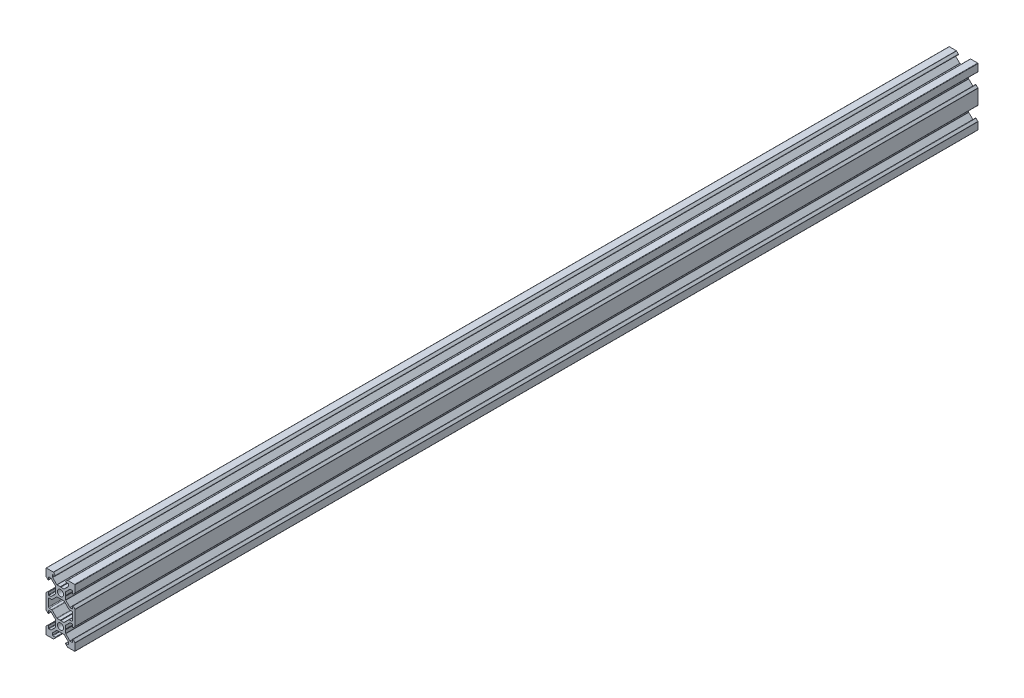
SolidWorks part; units mm, degrees
ref_plane "Front Plane" through (0, 0, 0) normal (0, 0, 1) x (1, 0, 0)
ref_plane "Top Plane" through (0, 0, 0) normal (0, 1, 0) x (1, 0, 0)
ref_plane "Right Plane" through (0, 0, 0) normal (1, 0, 0) x (0, 0, -1)
sketch "Sketch1" plane through (0, 0, 0) normal (0, 0, 1) x (1, 0, 0)
  line L0 (3.5607, 3.5607) -> (10.6317, 10.6317) construction
  line L1 (2.5, -3.5607) -> (-2.5, -3.5607)
  line L2 (3.5607, -2.5) -> (3.5607, 2.5)
  line L3 (2.5, 3.5607) -> (-2.5, 3.5607)
  line L4 (-3.5607, -2.5) -> (-3.5607, 2.5)
  line L5 (3.5607, -3.5607) -> (-3.5607, 3.5607) construction
  line L6 (3.5607, 3.5607) -> (-3.5607, -3.5607) construction
  line L7 (2.5, 3.5607) -> (5.5, 6.5607)
  line L8 (5.5, 6.5607) -> (5.5, 8.2521)
  line L9 (5.5, 8.2521) -> (3.1, 8.2521)
  line L10 (3.1, 8.2521) -> (4.8479, 10)
  line L11 (4.8479, 10) -> (10, 10)
  line L12 (3.5607, 2.5) -> (6.5607, 5.5)
  line L13 (6.5607, 5.5) -> (8.2521, 5.5)
  line L14 (8.2521, 5.5) -> (8.2521, 3.1)
  line L15 (8.2521, 3.1) -> (10, 4.8479)
  line L16 (10, 4.8479) -> (10, 10)
  line L17 (0, -55) -> (0, 55) construction
  line L18 (-3.5607, 3.5607) -> (-10.6317, 10.6317) construction
  line L19 (-10, 4.8479) -> (-10, 10)
  line L20 (-8.2521, 3.1) -> (-10, 4.8479)
  line L21 (-8.2521, 5.5) -> (-8.2521, 3.1)
  line L22 (-6.5607, 5.5) -> (-8.2521, 5.5)
  line L23 (-3.5607, 2.5) -> (-6.5607, 5.5)
  line L24 (-4.8479, 10) -> (-10, 10)
  line L25 (-3.1, 8.2521) -> (-4.8479, 10)
  line L26 (-5.5, 8.2521) -> (-3.1, 8.2521)
  line L27 (-5.5, 6.5607) -> (-5.5, 8.2521)
  line L28 (-2.5, 3.5607) -> (-5.5, 6.5607)
  line L29 (-8.2521, -7) -> (-5.9393, -7)
  line L30 (55, 0) -> (-55, 0) construction
  line L31 (-3.5607, -3.5607) -> (-10.6317, -10.6317) construction
  line L32 (3.5607, -3.5607) -> (10.6317, -10.6317) construction
  line L33 (-2.5, -3.5607) -> (-5.5, -6.5607)
  line L34 (-5.5, -6.5607) -> (-5.9393, -7)
  line L35 (5.5, -6.5607) -> (5.9393, -7)
  line L36 (8.2521, -7) -> (5.9393, -7)
  line L37 (-12.2633, -10) -> (14.5346, -10) construction
  line L38 (-3.5607, -2.5) -> (-6.5607, -5.5)
  line L39 (-6.5607, -5.5) -> (-8.2521, -5.5)
  line L40 (-8.2521, -5.5) -> (-8.2521, -3.1)
  line L41 (-8.2521, -3.1) -> (-10, -4.8479)
  line L42 (-10, -4.8479) -> (-10, -7)
  line L43 (10, -4.8479) -> (10, -7)
  line L44 (8.2521, -3.1) -> (10, -4.8479)
  line L45 (8.2521, -5.5) -> (8.2521, -3.1)
  line L46 (6.5607, -5.5) -> (8.2521, -5.5)
  line L47 (3.5607, -2.5) -> (6.5607, -5.5)
  line L48 (-3.5607, -23.5607) -> (-10.6317, -30.6317) construction
  line L49 (3.5607, -23.5607) -> (-3.5607, -16.4393) construction
  line L50 (3.5607, -16.4393) -> (-3.5607, -23.5607) construction
  line L51 (3.5607, -23.5607) -> (10.6317, -30.6317) construction
  line L52 (2.5, -3.5607) -> (5.5, -6.5607)
  line L53 (2.5, -16.4393) -> (5.5, -13.4393)
  line L54 (3.5607, -17.5) -> (6.5607, -14.5)
  line L55 (6.5607, -14.5) -> (8.2521, -14.5)
  line L56 (8.2521, -14.5) -> (8.2521, -16.9)
  line L57 (8.2521, -16.9) -> (10, -15.1521)
  line L58 (10, -15.1521) -> (10, -13)
  line L59 (-10, -15.1521) -> (-10, -13)
  line L60 (-8.2521, -16.9) -> (-10, -15.1521)
  line L61 (-8.2521, -14.5) -> (-8.2521, -16.9)
  line L62 (-6.5607, -14.5) -> (-8.2521, -14.5)
  line L63 (-3.5607, -17.5) -> (-6.5607, -14.5)
  line L64 (8.2521, -13) -> (5.9393, -13)
  line L65 (5.5, -13.4393) -> (5.9393, -13)
  line L66 (-5.5, -13.4393) -> (-5.9393, -13)
  line L67 (-2.5, -16.4393) -> (-5.5, -13.4393)
  line L68 (-8.2521, -13) -> (-5.9393, -13)
  line L69 (-2.5, -23.5607) -> (-5.5, -26.5607)
  line L70 (-5.5, -26.5607) -> (-5.5, -28.2521)
  line L71 (-5.5, -28.2521) -> (-3.1, -28.2521)
  line L72 (-3.1, -28.2521) -> (-4.8479, -30)
  line L73 (-4.8479, -30) -> (-10, -30)
  line L74 (-3.5607, -22.5) -> (-6.5607, -25.5)
  line L75 (-6.5607, -25.5) -> (-8.2521, -25.5)
  line L76 (-8.2521, -25.5) -> (-8.2521, -23.1)
  line L77 (-8.2521, -23.1) -> (-10, -24.8479)
  line L78 (-10, -24.8479) -> (-10, -30)
  line L79 (10, -24.8479) -> (10, -30)
  line L80 (8.2521, -23.1) -> (10, -24.8479)
  line L81 (8.2521, -25.5) -> (8.2521, -23.1)
  line L82 (6.5607, -25.5) -> (8.2521, -25.5)
  line L83 (3.5607, -22.5) -> (6.5607, -25.5)
  line L84 (4.8479, -30) -> (10, -30)
  line L85 (3.1, -28.2521) -> (4.8479, -30)
  line L86 (5.5, -28.2521) -> (3.1, -28.2521)
  line L87 (5.5, -26.5607) -> (5.5, -28.2521)
  line L88 (2.5, -23.5607) -> (5.5, -26.5607)
  line L89 (-3.5607, -17.5) -> (-3.5607, -22.5)
  line L90 (2.5, -23.5607) -> (-2.5, -23.5607)
  line L91 (3.5607, -17.5) -> (3.5607, -22.5)
  line L92 (2.5, -16.4393) -> (-2.5, -16.4393)
  line L93 (-10, -7) -> (-10, -13)
  line L94 (-8.2521, -13) -> (-8.2521, -7)
  line L95 (8.2521, -13) -> (8.2521, -7)
  line L96 (10, -7) -> (10, -13)
  circle A0 centre (0, 0) radius 2.1
  circle A1 centre (0, -20) radius 2.1
  point P0 (0, 0)
  point P102 (0, -20)
  dimension "D10" = 4.2
  dimension "D11" = 4.2
  dimension "D1" = 1.5
  dimension "D2" = 10
  dimension "D3" = 20
  dimension "D4" = 6.2
  dimension "D5" = 11
  dimension "D6" = 45
  dimension "D7" = 1.5
  dimension "D8" = 10
  dimension "D9" = 5
extrude "Boss-Extrude1" add sketch "Sketch1" along normal blind 622.69
fillet "Fillet1" radius 0.25 64 edges at (5.5, 6.5607, 311.345) (5.5, 8.2521, 311.345) (3.1, 8.2521, 311.345) (4.8479, 10, 311.345) (10, 10, 311.345) (10, 4.8479, 311.345) (8.2521, 3.1, 311.345) (8.2521, 5.5, 311.345) (6.5607, 5.5, 311.345) (3.5607, 2.5, 311.345) (3.5607, -2.5, 311.345) (6.5607, -5.5, 311.345) (8.2521, -5.5, 311.345) (8.2521, -3.1, 311.345) (10, -4.8479, 311.345) (10, -15.1521, 311.345) (8.2521, -16.9, 311.345) (8.2521, -14.5, 311.345) (6.5607, -14.5, 311.345) (3.5607, -17.5, 311.345) (3.5607, -22.5, 311.345) (6.5607, -25.5, 311.345) (8.2521, -25.5, 311.345) (8.2521, -23.1, 311.345) (10, -24.8479, 311.345) (10, -30, 311.345) (4.8479, -30, 311.345) (3.1, -28.2521, 311.345) (5.5, -28.2521, 311.345) (5.5, -26.5607, 311.345) (2.5, -23.5607, 311.345) (-2.5, -23.5607, 311.345) (-5.5, -26.5607, 311.345) (-5.5, -28.2521, 311.345) (-3.1, -28.2521, 311.345) (-4.8479, -30, 311.345) (-10, -30, 311.345) (-10, -24.8479, 311.345) (-8.2521, -23.1, 311.345) (-8.2521, -25.5, 311.345) (-6.5607, -25.5, 311.345) (-3.5607, -22.5, 311.345) (-3.5607, -17.5, 311.345) (-6.5607, -14.5, 311.345) (-8.2521, -14.5, 311.345) (-8.2521, -16.9, 311.345) (-10, -15.1521, 311.345) (-10, -4.8479, 311.345) (-8.2521, -3.1, 311.345) (-8.2521, -5.5, 311.345) (-6.5607, -5.5, 311.345) (-3.5607, -2.5, 311.345) (-3.5607, 2.5, 311.345) (-6.5607, 5.5, 311.345) (-8.2521, 5.5, 311.345) (-8.2521, 3.1, 311.345) (-10, 4.8479, 311.345) (-10, 10, 311.345) (-4.8479, 10, 311.345) (-5.5, 8.2521, 311.345) (-5.5, 6.5607, 311.345) (-2.5, 3.5607, 311.345) (2.5, 3.5607, 311.345) (-3.1, 8.2521, 311.345)
fillet "Fillet2" radius 0.5 12 edges at (-5.9393, -7, 311.345) (-8.2521, -7, 311.345) (-8.2521, -13, 311.345) (-5.9393, -13, 311.345) (-2.5, -16.4393, 311.345) (2.5, -16.4393, 311.345) (8.2521, -7, 311.345) (5.9393, -7, 311.345) (2.5, -3.5607, 311.345) (-2.5, -3.5607, 311.345) (5.9393, -13, 311.345) (8.2521, -13, 311.345)
sketch "Sketch2" plane through (0, 0, 622.69) normal (0, 0, 1) x (1, 0, 0)
  line L4 (0, 3.5607) -> (0, 3.1447) construction
  line L5 (2.3964, 3.5607) -> (-2.3964, 3.5607) construction
  line L6 (0, 3.399) -> (-0.2423, 3.5607)
  line L7 (0, 3.399) -> (0.2423, 3.5607)
  line L8 (-0.2423, 3.5607) -> (0.2423, 3.5607)
  line L9 (55, 0) -> (-55, 0) construction
  line L10 (0, -3.5607) -> (0, -3.1447) construction
  line L11 (0, -3.399) -> (0.2423, -3.5607)
  line L12 (0, -3.399) -> (-0.2423, -3.5607)
  line L13 (-0.2423, -3.5607) -> (0.2423, -3.5607)
  line L14 (0, 0) -> (-4.0856, 4.0856) construction
  line L15 (-8.2521, -10) -> (4.1581, -10) construction
  line L16 (-8.2521, -7.5) -> (-8.2521, -12.5) construction
  line L17 (3.5607, 0) -> (3.1447, 0) construction
  line L18 (3.5607, 0.2423) -> (3.5607, -0.2423)
  line L19 (3.399, 0) -> (3.5607, 0.2423)
  line L20 (3.399, 0) -> (3.5607, -0.2423)
  line L21 (-3.5607, 0) -> (-3.1447, 0) construction
  line L22 (-3.5607, 0.2423) -> (-3.5607, -0.2423)
  line L23 (-3.399, 0) -> (-3.5607, -0.2423)
  line L24 (-3.399, 0) -> (-3.5607, 0.2423)
  line L25 (-3.5607, -20) -> (-3.1447, -20) construction
  line L26 (3.5607, -20) -> (3.1447, -20) construction
  line L27 (0, -20) -> (-4.0856, -24.0856) construction
  line L28 (0, -16.4393) -> (0, -16.8553) construction
  line L29 (0, -23.5607) -> (0, -23.1447) construction
  line L30 (-3.399, -20) -> (-3.5607, -20.2423)
  line L31 (-3.399, -20) -> (-3.5607, -19.7577)
  line L32 (-3.5607, -20.2423) -> (-3.5607, -19.7577)
  line L33 (3.399, -20) -> (3.5607, -19.7577)
  line L34 (3.399, -20) -> (3.5607, -20.2423)
  line L35 (3.5607, -20.2423) -> (3.5607, -19.7577)
  line L36 (-0.2423, -16.4393) -> (0.2423, -16.4393)
  line L37 (0, -16.601) -> (-0.2423, -16.4393)
  line L38 (0, -16.601) -> (0.2423, -16.4393)
  line L39 (-0.2423, -23.5607) -> (0.2423, -23.5607)
  line L40 (0, -23.399) -> (0.2423, -23.5607)
  line L41 (0, -23.399) -> (-0.2423, -23.5607)
extrude "Cut-Extrude1" cut sketch "Sketch2" against normal through all
